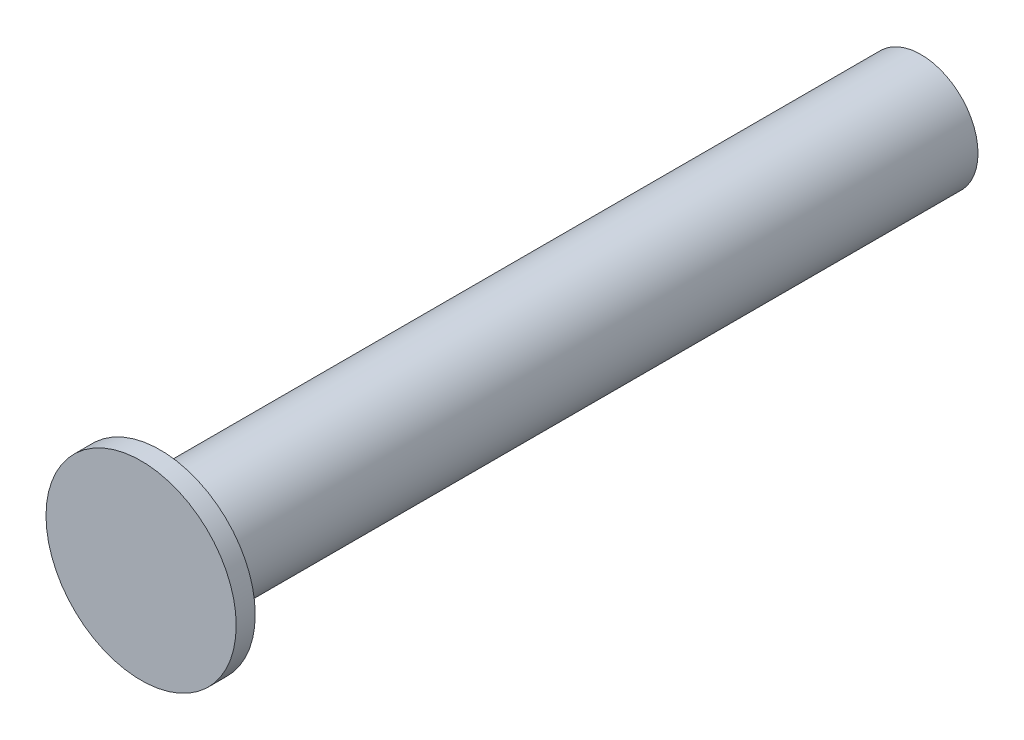
SolidWorks part; units mm, degrees
material "铸造合金钢"
ref_plane "前视基准面" through (0, 0, 0) normal (0, 0, 1) x (1, 0, 0)
ref_plane "上视基准面" through (0, 0, 0) normal (0, 1, 0) x (1, 0, 0)
ref_plane "右视基准面" through (0, 0, 0) normal (1, 0, 0) x (0, 0, -1)
sketch "草图1" plane through (0, 0, 0) normal (0, 0, 1) x (1, 0, 0)
  circle A0 centre (0, 0) radius 0.3
extrude "凸台-拉伸1" add sketch "草图1" along normal blind 4
sketch "草图2" plane through (0, 0, 4) normal (0, 0, 1) x (1, 0, 0)
  circle A0 centre (0, 0) radius 0.5
extrude "凸台-拉伸2" add sketch "草图2" along normal blind 0.1
